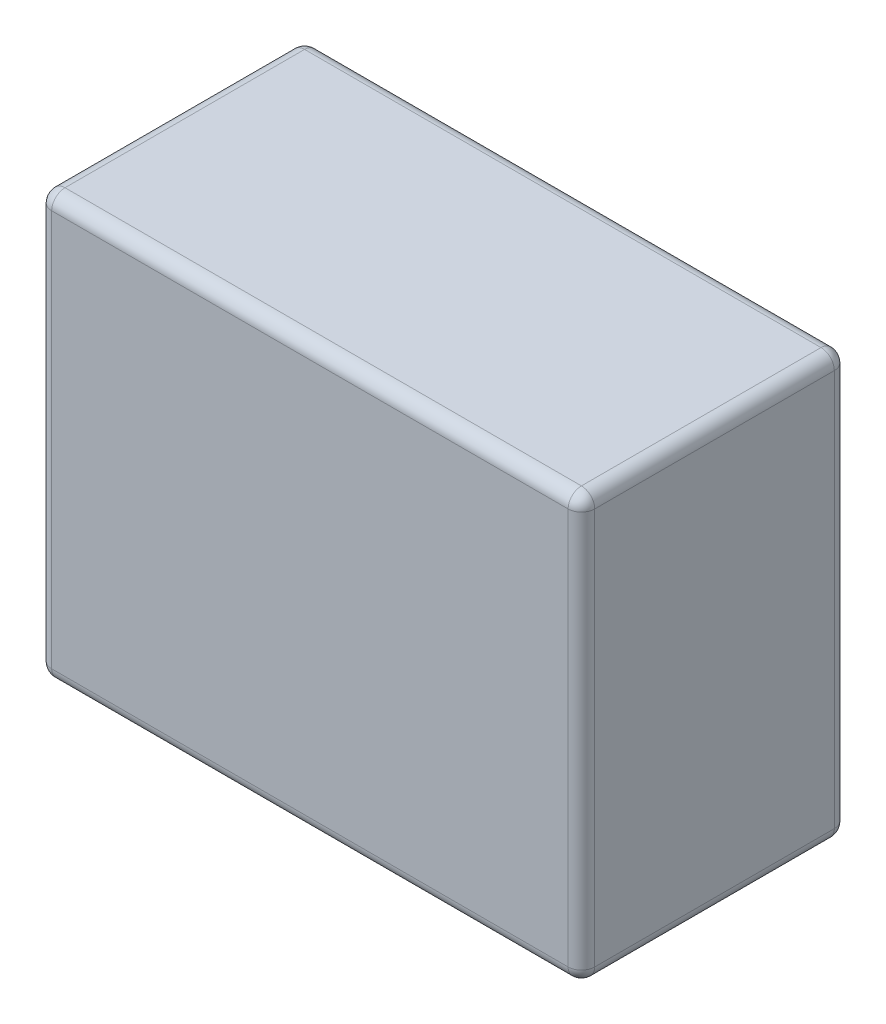
SolidWorks part; units mm, degrees
material "Custom Plastic"
ref_plane "Front Plane" through (0, 0, 0) normal (0, 0, 1) x (1, 0, 0)
ref_plane "Top Plane" through (0, 0, 0) normal (0, 1, 0) x (1, 0, 0)
ref_plane "Right Plane" through (0, 0, 0) normal (1, 0, 0) x (0, 0, -1)
sketch "Sketch1" plane through (0, 0, 0) normal (0, 1, 0) x (1, 0, 0)
  line L0 (-20.4, 10) -> (20.4, -10) construction
  line L1 (-20.4, 10) -> (20.4, 10)
  line L2 (-20.4, 10) -> (-20.4, -10)
  line L3 (-20.4, -10) -> (20.4, -10)
  line L4 (20.4, 10) -> (20.4, -10)
  dimension "D1" = 40.8
  dimension "D2" = 20
extrude "Boss-Extrude1" add sketch "Sketch1" along normal blind 36.4
sketch "Sketch2" plane through (0, 0, 0) normal (0, 1, 0) x (1, 0, 0)
  line L0 (-18.6242, 8.5) -> (18.6242, -8.5) construction
  line L1 (-20.4, 10) -> (20.4, 10)
  line L2 (-20.4, 10) -> (-20.4, -10)
  line L3 (-20.4, -10) -> (20.4, -10)
  line L4 (20.4, 10) -> (20.4, -10)
  line L5 (-18.6242, 8.5) -> (18.6242, 8.5)
  line L6 (-18.6242, 8.5) -> (-18.6242, -8.5)
  line L7 (-18.6242, -8.5) -> (18.6242, -8.5)
  line L8 (18.6242, 8.5) -> (18.6242, -8.5)
  dimension "D1" = 37.2485
  dimension "D2" = 17
extrude "Cut-Extrude1" cut sketch "Sketch2" along normal blind 4.6
sketch "Sketch3" plane through (0, 0, 0) normal (0, 1, 0) x (1, 0, 0)
  line L0 (0, 0) -> (18.6242, 0) construction
  line L1 (-18.6242, -8.5) -> (18.6242, -8.5)
  line L2 (-18.6242, -8.5) -> (-18.6242, 8.5)
  line L3 (-18.6242, 8.5) -> (18.6242, 8.5)
  line L4 (18.6242, -8.5) -> (18.6242, 8.5)
  circle A0 centre (9.3121, 0) radius 5
  dimension "D1" = 10
extrude "Cut-Extrude2" cut sketch "Sketch3" along normal blind 3.9
sketch "Sketch4" plane through (0, 0, 0) normal (0, 1, 0) x (1, 0, 0)
  circle A0 centre (9.3121, 0) radius 5
  circle A1 centre (9.3121, 0) radius 3.5
  dimension "D1" = 7
  dimension "D2" = 10
extrude "Cut-Extrude3" cut sketch "Sketch4" along normal blind 3
fillet "Fillet1" radius 1 12 edges at (-20.4, 20.5, 10) (20.4, 20.5, 10) (20.4, 20.5, -10) (-20.4, 20.5, -10) (-20.4, 4.6, 0) (0, 4.6, 10) (20.4, 4.6, 0) (0, 4.6, -10) (-20.4, 36.4, 0) (0, 36.4, 10) (20.4, 36.4, 0) (0, 36.4, -10)
fillet "Fillet2" radius 0.25 10 edges at (18.6242, 4.6, 0) (-18.6242, 4.6, 0) (18.6242, 4.25, -8.5) (0, 4.6, -8.5) (-18.6242, 4.25, -8.5) (0, 3.9, -8.5) (18.6242, 3.9, 0) (-18.6242, 3.9, 0) (0, 3.9, 8.5) (0, 4.6, 8.5)
